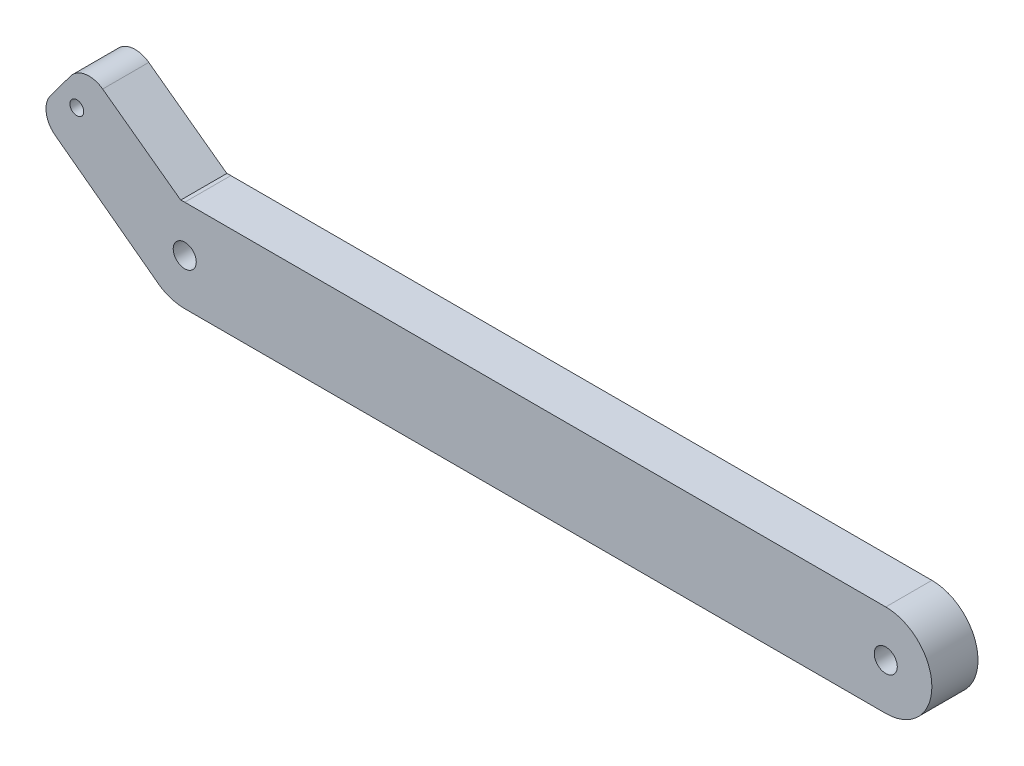
SolidWorks part; units mm, degrees
ref_plane "Plan de face" through (0, 0, 0) normal (0, 0, 1) x (1, 0, 0)
ref_plane "Plan de dessus" through (0, 0, 0) normal (0, 1, 0) x (1, 0, 0)
ref_plane "Plan de droite" through (0, 0, 0) normal (1, 0, 0) x (0, 0, -1)
sketch "Esquisse1" plane through (0, 0, 0) normal (0, 0, 1) x (1, 0, 0)
  line L0 (-5.3057, 1.5236) -> (-28.0759, 18.4888)
  line L1 (0, 0) -> (152, 0)
  line L3 (0, 20) -> (152, 20)
  line L4 (-29.0981, 25.4856) -> (-24.7625, 31.3047)
  line L5 (-17.7993, 32.3516) -> (-0.8766, 19.9615)
  line L6 (0, 10) -> (-23.4098, 26.0354) construction
  line L7 (0, 10) -> (-8.2741, 15.6677) construction
  line L8 (0, 10) -> (152, 10) construction
  arc A1 (152, 20) -> (152, 0) centre (152, 10) cw
  circle A2 centre (0, 10) radius 2.5
  circle A3 centre (152, 10) radius 2.5
  arc A4 (-29.0981, 25.4856) -> (-28.0759, 18.4888) centre (-25.0886, 22.4983) ccw
  arc A5 (-17.7993, 32.3516) -> (-24.7625, 31.3047) centre (-20.7531, 28.3173) ccw
  circle A6 centre (-23.4098, 26.0354) radius 1.5
  arc A7 (0, 0) -> (-5.3057, 1.5236) centre (0, 10) cw
  arc A8 (0, 20) -> (-0.8766, 19.9615) centre (0, 10) ccw
  dimension "D1" = 5
  dimension "D2" = 5
  dimension "D5" = 5
  dimension "D6" = 5
  dimension "D7" = 3
  dimension "D9" = 3
  dimension "D10" = 152
  dimension "D3" = 20
  dimension "D4" = 152
  dimension "D8" = 28.3752
extrude "Boss.-Extru.1" add sketch "Esquisse1" along normal blind 10
